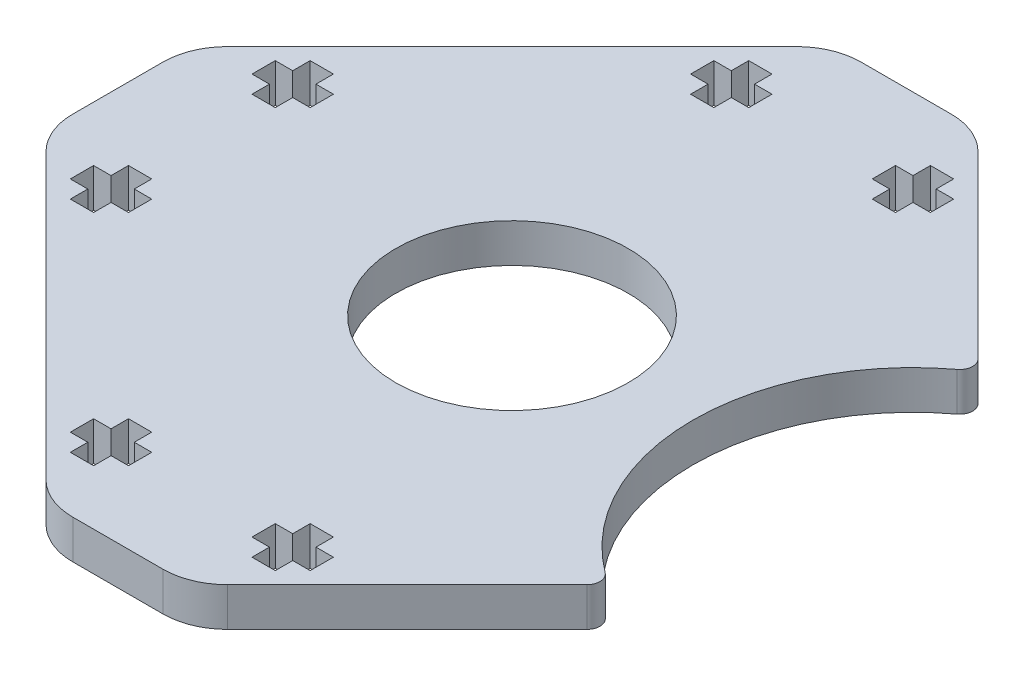
SolidWorks part; units mm, degrees
ref_plane "Front Plane" through (0, 0, 0) normal (0, 0, 1) x (1, 0, 0)
ref_plane "Top Plane" through (0, 0, 0) normal (0, 1, 0) x (1, 0, 0)
ref_plane "Right Plane" through (0, 0, 0) normal (1, 0, 0) x (0, 0, -1)
sketch "Sketch1" plane through (0, 0, 0) normal (0, 1, 0) x (1, 0, 0)
  line L0 (3.4914, 30.5) -> (-3.4914, 30.5)
  line L1 (-7.0269, 29.0355) -> (-29.0355, 7.0269)
  line L2 (-30.5, 3.4914) -> (-30.5, -3.4914)
  line L3 (-29.0355, -7.0269) -> (-7.0269, -29.0355)
  line L4 (-3.4914, -30.5) -> (3.4914, -30.5)
  line L5 (7.0269, -29.0355) -> (21.7799, -14.2825)
  line L7 (21.7799, 14.2825) -> (7.0269, 29.0355)
  arc A0 (7.0269, 29.0355) -> (3.4914, 30.5) centre (3.4914, 25.5) ccw
  arc A1 (-3.4914, 30.5) -> (-7.0269, 29.0355) centre (-3.4914, 25.5) ccw
  arc A2 (-29.0355, 7.0269) -> (-30.5, 3.4914) centre (-25.5, 3.4914) ccw
  arc A3 (-30.5, -3.4914) -> (-29.0355, -7.0269) centre (-25.5, -3.4914) ccw
  arc A4 (-7.0269, -29.0355) -> (-3.4914, -30.5) centre (-3.4914, -25.5) ccw
  arc A5 (3.4914, -30.5) -> (7.0269, -29.0355) centre (3.4914, -25.5) ccw
  circle A8 centre (0, 0) radius 9
  arc A9 (21.7799, -14.2825) -> (21.7799, 14.2825) centre (31, 0) cw
  dimension "D2" = 18
  dimension "D3" = 17
  dimension "D1" = 51
  dimension "D4" = 31
extrude "Boss-Extrude1" add sketch "Sketch1" along normal blind 3
sketch "Sketch4" plane through (0, 3, 0) normal (0, 1, 0) x (1, 0, 0)
  line L12 (-26.25, 7.9294) -> (-26.25, 6.1294)
  line L13 (-26.25, 6.1294) -> (-24.9, 6.1294)
  line L14 (-24.9, 6.1294) -> (-24.9, 4.7794)
  line L15 (-24.9, 4.7794) -> (-23.1, 4.7794)
  line L16 (-23.1, 4.7794) -> (-23.1, 6.1294)
  line L17 (-23.1, 6.1294) -> (-21.75, 6.1294)
  line L18 (-21.75, 6.1294) -> (-21.75, 7.9294)
  line L19 (-21.75, 7.9294) -> (-23.1, 7.9294)
  line L20 (-23.1, 7.9294) -> (-23.1, 9.2794)
  line L21 (-23.1, 9.2794) -> (-24.9, 9.2794)
  line L22 (-24.9, 9.2794) -> (-24.9, 7.9294)
  line L23 (-24.9, 7.9294) -> (-26.25, 7.9294)
  line L24 (-26.25, 7.9294) -> (-26.25, 6.1294)
  line L25 (-26.25, 6.1294) -> (-24.9, 6.1294)
  line L26 (-24.9, 6.1294) -> (-24.9, 4.7794)
  line L27 (-24.9, 4.7794) -> (-23.1, 4.7794)
  line L28 (-23.1, 4.7794) -> (-23.1, 6.1294)
  line L29 (-23.1, 6.1294) -> (-21.75, 6.1294)
  line L30 (-21.75, 6.1294) -> (-21.75, 7.9294)
  line L31 (-21.75, 7.9294) -> (-23.1, 7.9294)
  line L32 (-23.1, 7.9294) -> (-23.1, 9.2794)
  line L33 (-23.1, 9.2794) -> (-24.9, 9.2794)
  line L34 (-24.9, 9.2794) -> (-24.9, 7.9294)
  line L35 (-24.9, 7.9294) -> (-26.25, 7.9294)
  line L36 (-23.1, -4.7794) -> (-24.9, -4.7794)
  line L37 (-24.9, -4.7794) -> (-24.9, -6.1294)
  line L38 (-24.9, -6.1294) -> (-26.25, -6.1294)
  line L39 (-26.25, -6.1294) -> (-26.25, -7.9294)
  line L40 (-26.25, -7.9294) -> (-24.9, -7.9294)
  line L41 (-24.9, -7.9294) -> (-24.9, -9.2794)
  line L42 (-24.9, -9.2794) -> (-23.1, -9.2794)
  line L43 (-23.1, -9.2794) -> (-23.1, -7.9294)
  line L44 (-23.1, -7.9294) -> (-21.75, -7.9294)
  line L45 (-21.75, -7.9294) -> (-21.75, -6.1294)
  line L46 (-21.75, -6.1294) -> (-23.1, -6.1294)
  line L47 (-23.1, -6.1294) -> (-23.1, -4.7794)
  line L48 (-23.1, -4.7794) -> (-24.9, -4.7794)
  line L49 (-24.9, -4.7794) -> (-24.9, -6.1294)
  line L50 (-24.9, -6.1294) -> (-26.25, -6.1294)
  line L51 (-26.25, -6.1294) -> (-26.25, -7.9294)
  line L52 (-26.25, -7.9294) -> (-24.9, -7.9294)
  line L53 (-24.9, -7.9294) -> (-24.9, -9.2794)
  line L54 (-24.9, -9.2794) -> (-23.1, -9.2794)
  line L55 (-23.1, -9.2794) -> (-23.1, -7.9294)
  line L56 (-23.1, -7.9294) -> (-21.75, -7.9294)
  line L57 (-21.75, -7.9294) -> (-21.75, -6.1294)
  line L58 (-21.75, -6.1294) -> (-23.1, -6.1294)
  line L59 (-23.1, -6.1294) -> (-23.1, -4.7794)
  line L60 (7.9294, 23.1) -> (9.2794, 23.1)
  line L61 (9.2794, 23.1) -> (9.2794, 24.9)
  line L62 (9.2794, 24.9) -> (7.9294, 24.9)
  line L63 (7.9294, 24.9) -> (7.9294, 26.25)
  line L64 (7.9294, 26.25) -> (6.1294, 26.25)
  line L65 (6.1294, 26.25) -> (6.1294, 24.9)
  line L66 (6.1294, 24.9) -> (4.7794, 24.9)
  line L67 (4.7794, 24.9) -> (4.7794, 23.1)
  line L68 (4.7794, 23.1) -> (6.1294, 23.1)
  line L69 (6.1294, 23.1) -> (6.1294, 21.75)
  line L70 (6.1294, 21.75) -> (7.9294, 21.75)
  line L71 (7.9294, 21.75) -> (7.9294, 23.1)
  line L72 (7.9294, 23.1) -> (9.2794, 23.1)
  line L73 (9.2794, 23.1) -> (9.2794, 24.9)
  line L74 (9.2794, 24.9) -> (7.9294, 24.9)
  line L75 (7.9294, 24.9) -> (7.9294, 26.25)
  line L76 (7.9294, 26.25) -> (6.1294, 26.25)
  line L77 (6.1294, 26.25) -> (6.1294, 24.9)
  line L78 (6.1294, 24.9) -> (4.7794, 24.9)
  line L79 (4.7794, 24.9) -> (4.7794, 23.1)
  line L80 (4.7794, 23.1) -> (6.1294, 23.1)
  line L81 (6.1294, 23.1) -> (6.1294, 21.75)
  line L82 (6.1294, 21.75) -> (7.9294, 21.75)
  line L83 (7.9294, 21.75) -> (7.9294, 23.1)
  line L84 (26.25, -7.9294) -> (26.25, -6.1294)
  line L85 (26.25, -6.1294) -> (24.9, -6.1294)
  line L86 (24.9, -6.1294) -> (24.9, -4.7794)
  line L87 (24.9, -4.7794) -> (23.1, -4.7794)
  line L88 (23.1, -4.7794) -> (23.1, -6.1294)
  line L89 (23.1, -6.1294) -> (21.75, -6.1294)
  line L90 (21.75, -6.1294) -> (21.75, -7.9294)
  line L91 (21.75, -7.9294) -> (23.1, -7.9294)
  line L92 (23.1, -7.9294) -> (23.1, -9.2794)
  line L93 (23.1, -9.2794) -> (24.9, -9.2794)
  line L94 (24.9, -9.2794) -> (24.9, -7.9294)
  line L95 (24.9, -7.9294) -> (26.25, -7.9294)
  line L96 (26.25, -7.9294) -> (26.25, -6.1294)
  line L97 (26.25, -6.1294) -> (24.9, -6.1294)
  line L98 (24.9, -6.1294) -> (24.9, -4.7794)
  line L99 (24.9, -4.7794) -> (23.1, -4.7794)
  line L100 (23.1, -4.7794) -> (23.1, -6.1294)
  line L101 (23.1, -6.1294) -> (21.75, -6.1294)
  line L102 (21.75, -6.1294) -> (21.75, -7.9294)
  line L103 (21.75, -7.9294) -> (23.1, -7.9294)
  line L104 (23.1, -7.9294) -> (23.1, -9.2794)
  line L105 (23.1, -9.2794) -> (24.9, -9.2794)
  line L106 (24.9, -9.2794) -> (24.9, -7.9294)
  line L107 (24.9, -7.9294) -> (26.25, -7.9294)
  line L108 (-4.7794, 24.9) -> (-6.1294, 24.9)
  line L109 (-6.1294, 24.9) -> (-6.1294, 26.25)
  line L110 (-6.1294, 26.25) -> (-7.9294, 26.25)
  line L111 (-7.9294, 26.25) -> (-7.9294, 24.9)
  line L112 (-7.9294, 24.9) -> (-9.2794, 24.9)
  line L113 (-9.2794, 24.9) -> (-9.2794, 23.1)
  line L114 (-9.2794, 23.1) -> (-7.9294, 23.1)
  line L115 (-7.9294, 23.1) -> (-7.9294, 21.75)
  line L116 (-7.9294, 21.75) -> (-6.1294, 21.75)
  line L117 (-6.1294, 21.75) -> (-6.1294, 23.1)
  line L118 (-6.1294, 23.1) -> (-4.7794, 23.1)
  line L119 (-4.7794, 23.1) -> (-4.7794, 24.9)
  line L120 (-4.7794, 24.9) -> (-6.1294, 24.9)
  line L121 (-6.1294, 24.9) -> (-6.1294, 26.25)
  line L122 (-6.1294, 26.25) -> (-7.9294, 26.25)
  line L123 (-7.9294, 26.25) -> (-7.9294, 24.9)
  line L124 (-7.9294, 24.9) -> (-9.2794, 24.9)
  line L125 (-9.2794, 24.9) -> (-9.2794, 23.1)
  line L126 (-9.2794, 23.1) -> (-7.9294, 23.1)
  line L127 (-7.9294, 23.1) -> (-7.9294, 21.75)
  line L128 (-7.9294, 21.75) -> (-6.1294, 21.75)
  line L129 (-6.1294, 21.75) -> (-6.1294, 23.1)
  line L130 (-6.1294, 23.1) -> (-4.7794, 23.1)
  line L131 (-4.7794, 23.1) -> (-4.7794, 24.9)
  line L132 (26.25, 7.9294) -> (24.9, 7.9294)
  line L133 (26.25, 6.1294) -> (26.25, 7.9294)
  line L134 (24.9, 6.1294) -> (26.25, 6.1294)
  line L135 (24.9, 4.7794) -> (24.9, 6.1294)
  line L136 (23.1, 4.7794) -> (24.9, 4.7794)
  line L137 (23.1, 6.1294) -> (23.1, 4.7794)
  line L138 (21.75, 6.1294) -> (23.1, 6.1294)
  line L139 (21.75, 7.9294) -> (21.75, 6.1294)
  line L140 (23.1, 7.9294) -> (21.75, 7.9294)
  line L141 (23.1, 9.2794) -> (23.1, 7.9294)
  line L142 (24.9, 9.2794) -> (23.1, 9.2794)
  line L143 (24.9, 7.9294) -> (24.9, 9.2794)
  line L144 (26.25, 7.9294) -> (24.9, 7.9294)
  line L145 (26.25, 6.1294) -> (26.25, 7.9294)
  line L146 (24.9, 6.1294) -> (26.25, 6.1294)
  line L147 (24.9, 4.7794) -> (24.9, 6.1294)
  line L148 (23.1, 4.7794) -> (24.9, 4.7794)
  line L149 (23.1, 6.1294) -> (23.1, 4.7794)
  line L150 (21.75, 6.1294) -> (23.1, 6.1294)
  line L151 (21.75, 7.9294) -> (21.75, 6.1294)
  line L152 (23.1, 7.9294) -> (21.75, 7.9294)
  line L153 (23.1, 9.2794) -> (23.1, 7.9294)
  line L154 (24.9, 9.2794) -> (23.1, 9.2794)
  line L155 (24.9, 7.9294) -> (24.9, 9.2794)
  line L156 (-6.1294, -26.25) -> (-6.1294, -24.9)
  line L157 (-6.1294, -24.9) -> (-4.7794, -24.9)
  line L158 (-4.7794, -24.9) -> (-4.7794, -23.1)
  line L159 (-4.7794, -23.1) -> (-6.1294, -23.1)
  line L160 (-6.1294, -23.1) -> (-6.1294, -21.75)
  line L161 (-6.1294, -21.75) -> (-7.9294, -21.75)
  line L162 (-7.9294, -21.75) -> (-7.9294, -23.1)
  line L163 (-7.9294, -23.1) -> (-9.2794, -23.1)
  line L164 (-9.2794, -23.1) -> (-9.2794, -24.9)
  line L165 (-9.2794, -24.9) -> (-7.9294, -24.9)
  line L166 (-7.9294, -24.9) -> (-7.9294, -26.25)
  line L167 (-7.9294, -26.25) -> (-6.1294, -26.25)
  line L168 (-6.1294, -26.25) -> (-6.1294, -24.9)
  line L169 (-6.1294, -24.9) -> (-4.7794, -24.9)
  line L170 (-4.7794, -24.9) -> (-4.7794, -23.1)
  line L171 (-4.7794, -23.1) -> (-6.1294, -23.1)
  line L172 (-6.1294, -23.1) -> (-6.1294, -21.75)
  line L173 (-6.1294, -21.75) -> (-7.9294, -21.75)
  line L174 (-7.9294, -21.75) -> (-7.9294, -23.1)
  line L175 (-7.9294, -23.1) -> (-9.2794, -23.1)
  line L176 (-9.2794, -23.1) -> (-9.2794, -24.9)
  line L177 (-9.2794, -24.9) -> (-7.9294, -24.9)
  line L178 (-7.9294, -24.9) -> (-7.9294, -26.25)
  line L179 (-7.9294, -26.25) -> (-6.1294, -26.25)
  line L180 (7.9294, -26.25) -> (7.9294, -24.9)
  line L181 (7.9294, -24.9) -> (9.2794, -24.9)
  line L182 (9.2794, -24.9) -> (9.2794, -23.1)
  line L183 (9.2794, -23.1) -> (7.9294, -23.1)
  line L184 (7.9294, -23.1) -> (7.9294, -21.75)
  line L185 (7.9294, -21.75) -> (6.1294, -21.75)
  line L186 (6.1294, -21.75) -> (6.1294, -23.1)
  line L187 (6.1294, -23.1) -> (4.7794, -23.1)
  line L188 (4.7794, -23.1) -> (4.7794, -24.9)
  line L189 (4.7794, -24.9) -> (6.1294, -24.9)
  line L190 (6.1294, -24.9) -> (6.1294, -26.25)
  line L191 (6.1294, -26.25) -> (7.9294, -26.25)
  line L192 (7.9294, -26.25) -> (7.9294, -24.9)
  line L193 (7.9294, -24.9) -> (9.2794, -24.9)
  line L194 (9.2794, -24.9) -> (9.2794, -23.1)
  line L195 (9.2794, -23.1) -> (7.9294, -23.1)
  line L196 (7.9294, -23.1) -> (7.9294, -21.75)
  line L197 (7.9294, -21.75) -> (6.1294, -21.75)
  line L198 (6.1294, -21.75) -> (6.1294, -23.1)
  line L199 (6.1294, -23.1) -> (4.7794, -23.1)
  line L200 (4.7794, -23.1) -> (4.7794, -24.9)
  line L201 (4.7794, -24.9) -> (6.1294, -24.9)
  line L202 (6.1294, -24.9) -> (6.1294, -26.25)
  line L203 (6.1294, -26.25) -> (7.9294, -26.25)
  dimension "D1" = 0
  dimension "D2" = 0
  dimension "D3" = 0
  dimension "D4" = 0
  dimension "D5" = 0
  dimension "D6" = 0
  dimension "D7" = 0
  dimension "D8" = 0
extrude "Cut-Extrude1" cut sketch "Sketch4" against normal through all
fillet "Fillet1" radius 1 2 edges at (21.7799, 1.5, 14.2825) (21.7799, 1.5, -14.2825)
sketch "Sketch5" plane through (0, 3, 0) normal (0, 1, 0) x (1, 0, 0)
  line L7 (7.0269, -29.0355) -> (20.9347, -15.1278)
  line L8 (20.9347, 15.1278) -> (7.0269, 29.0355)
  line L9 (3.4914, 30.5) -> (-3.4914, 30.5)
  line L10 (-7.0269, 29.0355) -> (-29.0355, 7.0269)
  line L11 (-30.5, 3.4914) -> (-30.5, -3.4914)
  line L12 (7.9294, -24.9) -> (9.2794, -24.9)
  line L13 (7.9294, -26.25) -> (7.9294, -24.9)
  line L14 (6.1294, -26.25) -> (7.9294, -26.25)
  line L15 (6.1294, -24.9) -> (6.1294, -26.25)
  line L16 (4.7794, -24.9) -> (6.1294, -24.9)
  line L17 (4.7794, -23.1) -> (4.7794, -24.9)
  line L18 (6.1294, -23.1) -> (4.7794, -23.1)
  line L19 (6.1294, -21.75) -> (6.1294, -23.1)
  line L20 (7.9294, -21.75) -> (6.1294, -21.75)
  line L21 (7.9294, -23.1) -> (7.9294, -21.75)
  line L22 (9.2794, -23.1) -> (7.9294, -23.1)
  line L23 (9.2794, -24.9) -> (9.2794, -23.1)
  line L24 (7.9294, -24.9) -> (9.2794, -24.9)
  line L25 (7.9294, -26.25) -> (7.9294, -24.9)
  line L26 (6.1294, -26.25) -> (7.9294, -26.25)
  line L27 (6.1294, -24.9) -> (6.1294, -26.25)
  line L28 (4.7794, -24.9) -> (6.1294, -24.9)
  line L29 (4.7794, -23.1) -> (4.7794, -24.9)
  line L30 (6.1294, -23.1) -> (4.7794, -23.1)
  line L31 (6.1294, -21.75) -> (6.1294, -23.1)
  line L32 (7.9294, -21.75) -> (6.1294, -21.75)
  line L33 (7.9294, -23.1) -> (7.9294, -21.75)
  line L34 (9.2794, -23.1) -> (7.9294, -23.1)
  line L35 (9.2794, -24.9) -> (9.2794, -23.1)
  line L36 (-6.1294, 24.9) -> (-6.1294, 26.25)
  line L37 (-4.7794, 24.9) -> (-6.1294, 24.9)
  line L38 (-4.7794, 23.1) -> (-4.7794, 24.9)
  line L39 (-6.1294, 23.1) -> (-4.7794, 23.1)
  line L40 (-6.1294, 21.75) -> (-6.1294, 23.1)
  line L41 (-7.9294, 21.75) -> (-6.1294, 21.75)
  line L42 (-7.9294, 23.1) -> (-7.9294, 21.75)
  line L43 (-9.2794, 23.1) -> (-7.9294, 23.1)
  line L44 (-9.2794, 24.9) -> (-9.2794, 23.1)
  line L45 (-7.9294, 24.9) -> (-9.2794, 24.9)
  line L46 (-7.9294, 26.25) -> (-7.9294, 24.9)
  line L47 (-6.1294, 26.25) -> (-7.9294, 26.25)
  line L48 (-6.1294, 24.9) -> (-6.1294, 26.25)
  line L49 (-4.7794, 24.9) -> (-6.1294, 24.9)
  line L50 (-4.7794, 23.1) -> (-4.7794, 24.9)
  line L51 (-6.1294, 23.1) -> (-4.7794, 23.1)
  line L52 (-6.1294, 21.75) -> (-6.1294, 23.1)
  line L53 (-7.9294, 21.75) -> (-6.1294, 21.75)
  line L54 (-7.9294, 23.1) -> (-7.9294, 21.75)
  line L55 (-9.2794, 23.1) -> (-7.9294, 23.1)
  line L56 (-9.2794, 24.9) -> (-9.2794, 23.1)
  line L57 (-7.9294, 24.9) -> (-9.2794, 24.9)
  line L58 (-7.9294, 26.25) -> (-7.9294, 24.9)
  line L59 (-6.1294, 26.25) -> (-7.9294, 26.25)
  line L60 (-24.9, 7.9294) -> (-26.25, 7.9294)
  line L61 (-24.9, 9.2794) -> (-24.9, 7.9294)
  line L62 (-23.1, 9.2794) -> (-24.9, 9.2794)
  line L63 (-23.1, 7.9294) -> (-23.1, 9.2794)
  line L64 (-21.75, 7.9294) -> (-23.1, 7.9294)
  line L65 (-21.75, 6.1294) -> (-21.75, 7.9294)
  line L66 (-23.1, 6.1294) -> (-21.75, 6.1294)
  line L67 (-23.1, 4.7794) -> (-23.1, 6.1294)
  line L68 (-24.9, 4.7794) -> (-23.1, 4.7794)
  line L69 (-24.9, 6.1294) -> (-24.9, 4.7794)
  line L70 (-26.25, 6.1294) -> (-24.9, 6.1294)
  line L71 (-26.25, 7.9294) -> (-26.25, 6.1294)
  line L72 (-24.9, 7.9294) -> (-26.25, 7.9294)
  line L73 (-24.9, 9.2794) -> (-24.9, 7.9294)
  line L74 (-23.1, 9.2794) -> (-24.9, 9.2794)
  line L75 (-23.1, 7.9294) -> (-23.1, 9.2794)
  line L76 (-21.75, 7.9294) -> (-23.1, 7.9294)
  line L77 (-21.75, 6.1294) -> (-21.75, 7.9294)
  line L78 (-23.1, 6.1294) -> (-21.75, 6.1294)
  line L79 (-23.1, 4.7794) -> (-23.1, 6.1294)
  line L80 (-24.9, 4.7794) -> (-23.1, 4.7794)
  line L81 (-24.9, 6.1294) -> (-24.9, 4.7794)
  line L82 (-26.25, 6.1294) -> (-24.9, 6.1294)
  line L83 (-26.25, 7.9294) -> (-26.25, 6.1294)
  line L84 (-7.9294, -26.25) -> (-6.1294, -26.25)
  line L85 (-7.9294, -24.9) -> (-7.9294, -26.25)
  line L86 (-9.2794, -24.9) -> (-7.9294, -24.9)
  line L87 (-9.2794, -23.1) -> (-9.2794, -24.9)
  line L88 (-7.9294, -23.1) -> (-9.2794, -23.1)
  line L89 (-7.9294, -21.75) -> (-7.9294, -23.1)
  line L90 (-6.1294, -21.75) -> (-7.9294, -21.75)
  line L91 (-6.1294, -23.1) -> (-6.1294, -21.75)
  line L92 (-4.7794, -23.1) -> (-6.1294, -23.1)
  line L93 (-4.7794, -24.9) -> (-4.7794, -23.1)
  line L94 (-6.1294, -24.9) -> (-4.7794, -24.9)
  line L95 (-6.1294, -26.25) -> (-6.1294, -24.9)
  line L96 (-7.9294, -26.25) -> (-6.1294, -26.25)
  line L97 (-7.9294, -24.9) -> (-7.9294, -26.25)
  line L98 (-9.2794, -24.9) -> (-7.9294, -24.9)
  line L99 (-9.2794, -23.1) -> (-9.2794, -24.9)
  line L100 (-7.9294, -23.1) -> (-9.2794, -23.1)
  line L101 (-7.9294, -21.75) -> (-7.9294, -23.1)
  line L102 (-6.1294, -21.75) -> (-7.9294, -21.75)
  line L103 (-6.1294, -23.1) -> (-6.1294, -21.75)
  line L104 (-4.7794, -23.1) -> (-6.1294, -23.1)
  line L105 (-4.7794, -24.9) -> (-4.7794, -23.1)
  line L106 (-6.1294, -24.9) -> (-4.7794, -24.9)
  line L107 (-6.1294, -26.25) -> (-6.1294, -24.9)
  line L108 (-24.9, -4.7794) -> (-24.9, -6.1294)
  line L109 (-23.1, -4.7794) -> (-24.9, -4.7794)
  line L110 (-23.1, -6.1294) -> (-23.1, -4.7794)
  line L111 (-21.75, -6.1294) -> (-23.1, -6.1294)
  line L112 (-21.75, -7.9294) -> (-21.75, -6.1294)
  line L113 (-23.1, -7.9294) -> (-21.75, -7.9294)
  line L114 (-23.1, -9.2794) -> (-23.1, -7.9294)
  line L115 (-24.9, -9.2794) -> (-23.1, -9.2794)
  line L116 (-24.9, -7.9294) -> (-24.9, -9.2794)
  line L117 (-26.25, -7.9294) -> (-24.9, -7.9294)
  line L118 (-26.25, -6.1294) -> (-26.25, -7.9294)
  line L119 (-24.9, -6.1294) -> (-26.25, -6.1294)
  line L120 (-24.9, -4.7794) -> (-24.9, -6.1294)
  line L121 (-23.1, -4.7794) -> (-24.9, -4.7794)
  line L122 (-23.1, -6.1294) -> (-23.1, -4.7794)
  line L123 (-21.75, -6.1294) -> (-23.1, -6.1294)
  line L124 (-21.75, -7.9294) -> (-21.75, -6.1294)
  line L125 (-23.1, -7.9294) -> (-21.75, -7.9294)
  line L126 (-23.1, -9.2794) -> (-23.1, -7.9294)
  line L127 (-24.9, -9.2794) -> (-23.1, -9.2794)
  line L128 (-24.9, -7.9294) -> (-24.9, -9.2794)
  line L129 (-26.25, -7.9294) -> (-24.9, -7.9294)
  line L130 (-26.25, -6.1294) -> (-26.25, -7.9294)
  line L131 (-24.9, -6.1294) -> (-26.25, -6.1294)
  line L132 (7.9294, 21.75) -> (7.9294, 23.1)
  line L133 (6.1294, 21.75) -> (7.9294, 21.75)
  line L134 (6.1294, 23.1) -> (6.1294, 21.75)
  line L135 (4.7794, 23.1) -> (6.1294, 23.1)
  line L136 (4.7794, 24.9) -> (4.7794, 23.1)
  line L137 (6.1294, 24.9) -> (4.7794, 24.9)
  line L138 (6.1294, 26.25) -> (6.1294, 24.9)
  line L139 (7.9294, 26.25) -> (6.1294, 26.25)
  line L140 (7.9294, 24.9) -> (7.9294, 26.25)
  line L141 (9.2794, 24.9) -> (7.9294, 24.9)
  line L142 (9.2794, 23.1) -> (9.2794, 24.9)
  line L143 (7.9294, 23.1) -> (9.2794, 23.1)
  line L144 (7.9294, 21.75) -> (7.9294, 23.1)
  line L145 (6.1294, 21.75) -> (7.9294, 21.75)
  line L146 (6.1294, 23.1) -> (6.1294, 21.75)
  line L147 (4.7794, 23.1) -> (6.1294, 23.1)
  line L148 (4.7794, 24.9) -> (4.7794, 23.1)
  line L149 (6.1294, 24.9) -> (4.7794, 24.9)
  line L150 (6.1294, 26.25) -> (6.1294, 24.9)
  line L151 (7.9294, 26.25) -> (6.1294, 26.25)
  line L152 (7.9294, 24.9) -> (7.9294, 26.25)
  line L153 (9.2794, 24.9) -> (7.9294, 24.9)
  line L154 (9.2794, 23.1) -> (9.2794, 24.9)
  line L155 (7.9294, 23.1) -> (9.2794, 23.1)
  line L156 (-29.0355, -7.0269) -> (-7.0269, -29.0355)
  line L157 (-3.4914, -30.5) -> (3.4914, -30.5)
  line L158 (7.0269, -29.0355) -> (20.9347, -15.1278)
  line L159 (20.9347, 15.1278) -> (7.0269, 29.0355)
  line L160 (3.4914, 30.5) -> (-3.4914, 30.5)
  line L161 (-7.0269, 29.0355) -> (-29.0355, 7.0269)
  line L162 (-30.5, 3.4914) -> (-30.5, -3.4914)
  line L163 (-29.0355, -7.0269) -> (-7.0269, -29.0355)
  line L164 (-3.4914, -30.5) -> (3.4914, -30.5)
  circle A1 centre (0, 0) radius 9
  circle A2 centre (0, 0) radius 9
  arc A11 (20.9347, -15.1278) -> (20.8261, -13.6195) centre (20.2276, -14.4206) ccw
  arc A12 (20.8261, 13.6195) -> (20.8261, -13.6195) centre (31, 0) ccw
  arc A13 (20.8261, 13.6195) -> (20.9347, 15.1278) centre (20.2276, 14.4206) ccw
  arc A14 (7.0269, 29.0355) -> (3.4914, 30.5) centre (3.4914, 25.5) ccw
  arc A15 (-3.4914, 30.5) -> (-7.0269, 29.0355) centre (-3.4914, 25.5) ccw
  arc A16 (-29.0355, 7.0269) -> (-30.5, 3.4914) centre (-25.5, 3.4914) ccw
  arc A17 (-30.5, -3.4914) -> (-29.0355, -7.0269) centre (-25.5, -3.4914) ccw
  arc A18 (-7.0269, -29.0355) -> (-3.4914, -30.5) centre (-3.4914, -25.5) ccw
  arc A19 (3.4914, -30.5) -> (7.0269, -29.0355) centre (3.4914, -25.5) ccw
  arc A20 (20.9347, -15.1278) -> (20.8261, -13.6195) centre (20.2276, -14.4206) ccw
  arc A21 (20.8261, 13.6195) -> (20.8261, -13.6195) centre (31, 0) ccw
  arc A22 (20.8261, 13.6195) -> (20.9347, 15.1278) centre (20.2276, 14.4206) ccw
  arc A23 (7.0269, 29.0355) -> (3.4914, 30.5) centre (3.4914, 25.5) ccw
  arc A24 (-3.4914, 30.5) -> (-7.0269, 29.0355) centre (-3.4914, 25.5) ccw
  arc A25 (-29.0355, 7.0269) -> (-30.5, 3.4914) centre (-25.5, 3.4914) ccw
  arc A26 (-30.5, -3.4914) -> (-29.0355, -7.0269) centre (-25.5, -3.4914) ccw
  arc A27 (-7.0269, -29.0355) -> (-3.4914, -30.5) centre (-3.4914, -25.5) ccw
  arc A28 (3.4914, -30.5) -> (7.0269, -29.0355) centre (3.4914, -25.5) ccw
  dimension "D1" = 0
  dimension "D2" = 0
  dimension "D3" = 0
  dimension "D4" = 0
  dimension "D5" = 0
  dimension "D6" = 0
  dimension "D7" = 0
  dimension "D8" = 0
